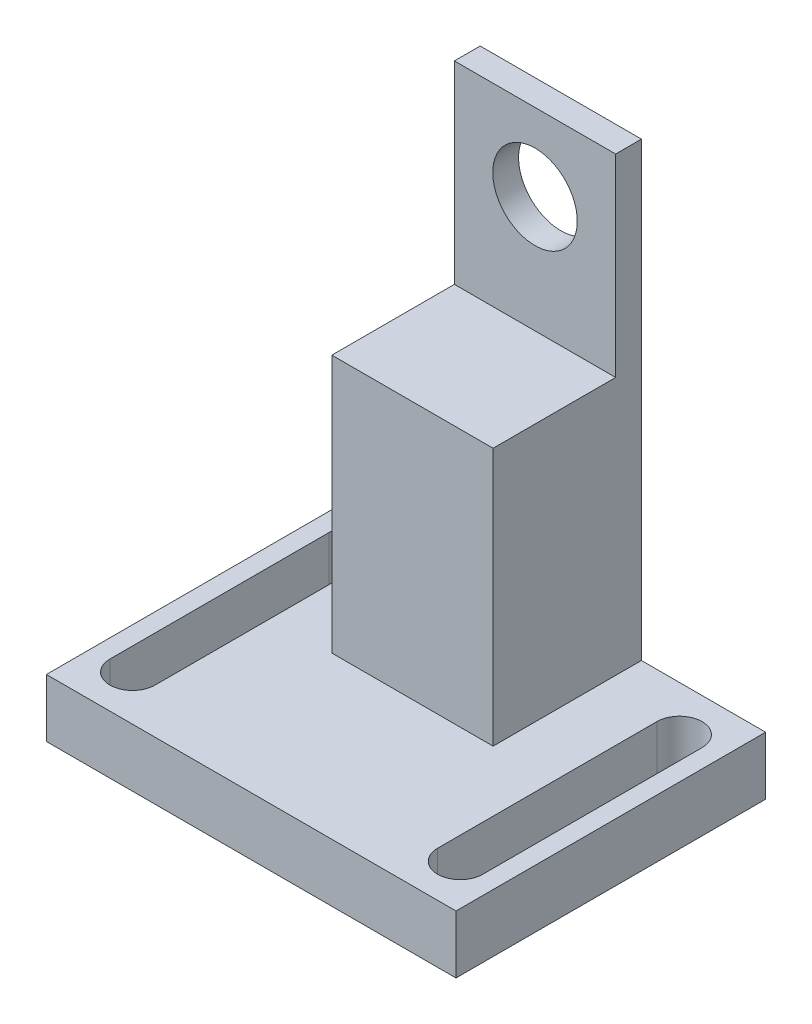
SolidWorks part; units mm, degrees
material "AISI 304"
ref_plane "Front Plane" through (0, 0, 0) normal (0, 0, 1) x (1, 0, 0)
ref_plane "Top Plane" through (0, 0, 0) normal (0, 1, 0) x (1, 0, 0)
ref_plane "Right Plane" through (0, 0, 0) normal (1, 0, 0) x (0, 0, -1)
sketch "Sketch1" plane through (0, 0, 0) normal (0, 0, 1) x (1, 0, 0)
  line L0 (-12.5, -58) -> (-31.75, -58)
  line L1 (-12.5, 12) -> (12.5, 12)
  line L2 (-12.5, 12) -> (-12.5, -58)
  line L3 (-31.75, -58) -> (-31.75, -67)
  line L4 (12.5, 12) -> (12.5, -58)
  line L5 (-31.75, -67) -> (31.75, -67)
  line L6 (12.5, -58) -> (31.75, -58)
  line L7 (31.75, -58) -> (31.75, -67)
  line L8 (0, 12) -> (0, 0) construction
  line L9 (0, 0) -> (0, -67) construction
  circle A0 centre (0, 0) radius 6.55
  dimension "D1" = 13.1
  dimension "D2" = 12
  dimension "D3" = 67
  dimension "D4" = 25
  dimension "D5" = 63.5
  dimension "D6" = 9
extrude "Boss-Extrude1" add sketch "Sketch1" along normal mid plane 23
sketch "Sketch9" plane through (-12.5, 0, 0) normal (-1, 0, 0) x (0, 0, 1)
  line L0 (-7.5, 12) -> (-7.5, -18)
  line L1 (11.5, 12) -> (-11.5, 12) construction
  line L2 (-7.5, -18) -> (11.5, -18)
  line L3 (11.5, 12) -> (11.5, -58) construction
  line L4 (11.5, -18) -> (11.5, 12)
  line L5 (11.5, 12) -> (-7.5, 12)
  line L6 (-11.5, 12) -> (-11.5, -58) construction
  dimension "D1" = 4
  dimension "D2" = 18
extrude "Cut-Extrude4" cut sketch "Sketch9" against normal through all
sketch "Sketch12" plane through (0, 0, 11.5) normal (0, 0, 1) x (1, 0, 0)
  line L1 (-31.75, -67) -> (31.75, -67)
  line L2 (-31.75, -67) -> (-31.75, -58)
  line L3 (-31.75, -58) -> (31.75, -58)
  line L4 (31.75, -67) -> (31.75, -58)
extrude "Boss-Extrude2" add sketch "Sketch12" along normal blind 25
sketch "Sketch11" plane through (0, -67, 0) normal (0, -1, 0) x (1, 0, 0)
  line L0 (-25.4, 29.5) -> (-25.4, -4.5) construction
  line L1 (-21.9, 29.5) -> (-21.9, -4.5)
  line L2 (-28.9, 29.5) -> (-28.9, -4.5)
  line L3 (25.4, -4.5) -> (25.4, 29.5) construction
  line L4 (21.9, -4.5) -> (21.9, 29.5)
  line L5 (28.9, -4.5) -> (28.9, 29.5)
  line L6 (-25.4, 12.5) -> (25.4, 12.5) construction
  line L8 (0, -11.5) -> (0, 12.5) construction
  line L9 (-31.75, -11.5) -> (31.75, -11.5) construction
  line L10 (-31.75, 36.5) -> (31.75, 36.5) construction
  line L11 (0, 12.5) -> (0, 36.5) construction
  arc A0 (-21.9, 29.5) -> (-28.9, 29.5) centre (-25.4, 29.5) ccw
  arc A1 (-28.9, -4.5) -> (-21.9, -4.5) centre (-25.4, -4.5) ccw
  arc A2 (21.9, -4.5) -> (28.9, -4.5) centre (25.4, -4.5) ccw
  arc A3 (28.9, 29.5) -> (21.9, 29.5) centre (25.4, 29.5) ccw
  point P2 (-25.4, 12.5)
  point P8 (25.4, 12.5)
  dimension "D1" = 7
  dimension "D2" = 50.8
  dimension "D3" = 7
extrude "Cut-Extrude5" cut sketch "Sketch11" against normal through all
